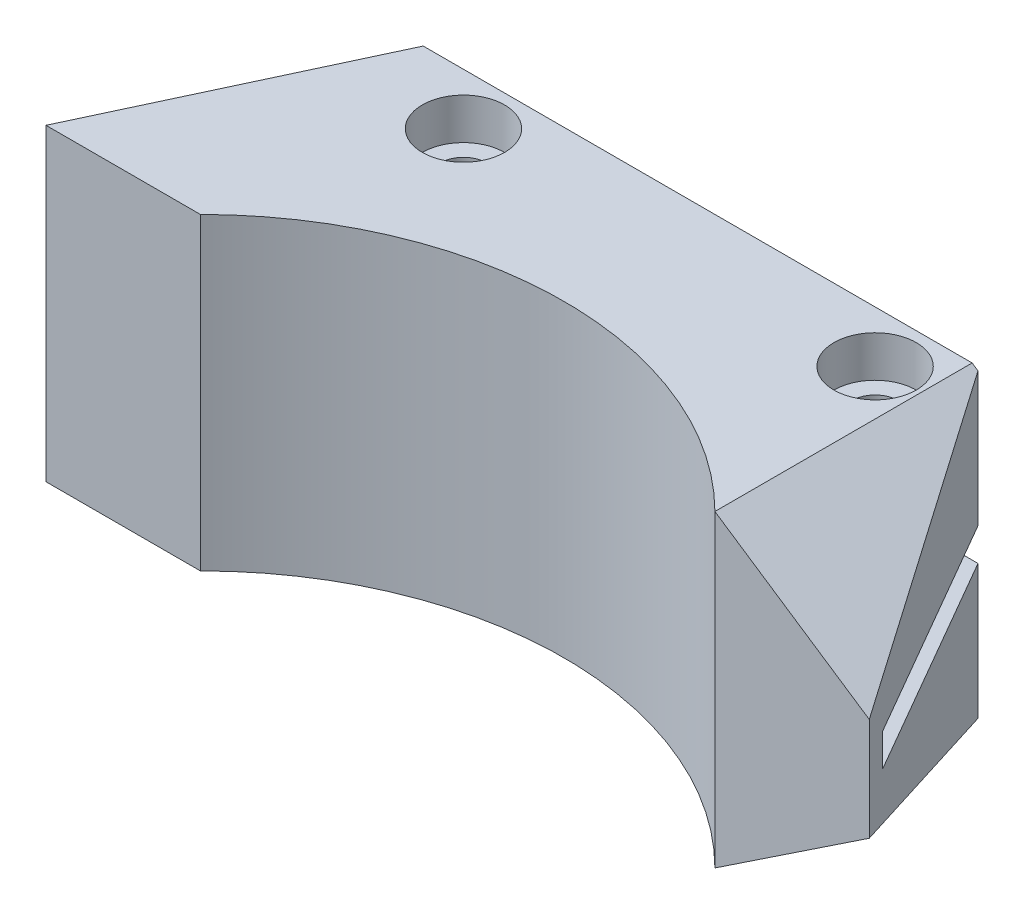
SolidWorks part; units mm, degrees
material "ABS"
ref_plane "Front Plane" through (0, 0, 0) normal (0, 0, 1) x (1, 0, 0)
ref_plane "Top Plane" through (0, 0, 0) normal (0, 1, 0) x (1, 0, 0)
ref_plane "Right Plane" through (0, 0, 0) normal (1, 0, 0) x (0, 0, -1)
sketch "Sketch1" plane through (0, 0, 0) normal (0, 1, 0) x (1, 0, 0)
  line L0 (0, 0) -> (-15, 0)
  line L1 (0, 0) -> (-14.4338, 25)
  line L2 (-14.4338, 25) -> (-68.3423, 25)
  line L3 (-68.3423, 25) -> (-80, 0)
  line L4 (-80, 0) -> (-65, 0)
  arc A0 (-65, 0) -> (-15, 0) centre (-40, -25) cw
  point P8 (-66.6482, 30)
  dimension "D1" = 15
  dimension "D2" = 15
  dimension "D3" = 50
  dimension "D4" = 120
  dimension "D5" = 25
  dimension "D6" = 90
  dimension "D7" = 115
extrude "Boss-Extrude1" add sketch "Sketch1" along normal mid plane 30
sketch "Sketch2" plane through (0, 0, 0) normal (0, 1, 0) x (1, 0, 0)
  line L0 (-1.7321, 3) -> (-13.2791, 3)
  line L1 (0, 0) -> (-14.4338, 25) construction
  line L2 (-13.2791, 3) -> (-19.2907, 13.4125)
  line L3 (-22.0403, 15) -> (-73.0054, 15)
  line L4 (-68.3423, 25) -> (-80, 0) construction
  line L5 (-14.4338, 25) -> (-68.3423, 25) construction
  line L6 (-15, 0) -> (0, 0) construction
  line L12 (0, 0) -> (-14.4338, 25)
  line L13 (-14.4338, 25) -> (-68.3423, 25)
  line L14 (-68.3423, 25) -> (-80, 0)
  line L15 (-80, 0) -> (-65, 0)
  line L16 (-15, 0) -> (0, 0)
  line L17 (0, 0) -> (-14.4338, 25)
  line L18 (-14.4338, 25) -> (-68.3423, 25)
  line L19 (-68.3423, 25) -> (-80, 0)
  line L20 (-80, 0) -> (-65, 0)
  line L21 (-15, 0) -> (0, 0)
  arc A0 (-19.2907, 13.4125) -> (-22.0403, 15) centre (-22.0403, 11.825) ccw
  arc A1 (-15, 0) -> (-65, 0) centre (-40, -25) ccw
  arc A2 (-15, 0) -> (-65, 0) centre (-40, -25) ccw
  dimension "D5" = 3.175
  dimension "D1" = 10
  dimension "D2" = 10
  dimension "D3" = 3
  dimension "D4" = 0
extrude "Cut-Extrude1" cut sketch "Sketch2" against normal blind 1.5875 and the other way blind 1.5875 contours A0 L2 L0 L17 L18 L19 L3
sketch "Sketch5" plane through (0, 15, 0) normal (0, 1, 0) x (1, 0, 0)
  line L0 (-14.4338, 25) -> (-68.3423, 25) construction
  point P0 (-59.4338, 20)
  point P2 (-19.4338, 20)
  point P5 (0, 0)
  dimension "D1" = 5
  dimension "D2" = 5
  dimension "D3" = 40
hole_wizard "CBORE for M4 SHCS1" positions "Sketch5" profile "Sketch6" counterbore size "M4" standard "ANSI Metric" end condition through all
sketch "Sketch6" plane through (-59.4338, 15, -20) normal (1, 0, 0) x (0, 0, 1)
  line L0 (0, 0) -> (0, 30)
  line L1 (0, 30) -> (2.25, 30)
  line L3 (2.25, 30) -> (2.25, 4)
  line L4 (2.25, 4) -> (4, 4)
  line L5 (4, 4) -> (4, 0)
  line L7 (4, 0) -> (0, 0)
  line L11 (0, -6.35) -> (0, 107.95) construction
  dimension "Thru Hole Dia." = 4.5
  dimension "Thru Hole Depth" = 30
  dimension "C'Bore Dia." = 8
  dimension "C'Bore Depth" = 4
sketch "Sketch7" plane through (0, 0, 0) normal (0, 0, 1) x (1, 0, 0)
  line L0 (0, 5) -> (-15, 15)
  line L1 (0, 15) -> (0, -15) construction
  line L2 (-15, 15) -> (0, 15) construction
  line L3 (-15, 15) -> (0, 15)
  line L4 (0, 15) -> (0, 5)
  line L5 (0, -15) -> (-15, -15)
  line L6 (-15, -15) -> (0, -15) construction
  line L7 (-15, -15) -> (0, -5)
  line L8 (0, -5) -> (0, -15)
  point P13 (-9.9215, -15)
  dimension "D1" = 5
  dimension "D2" = 5
  dimension "D3" = 15
extrude "Cut-Extrude2" cut sketch "Sketch7" against normal through all
